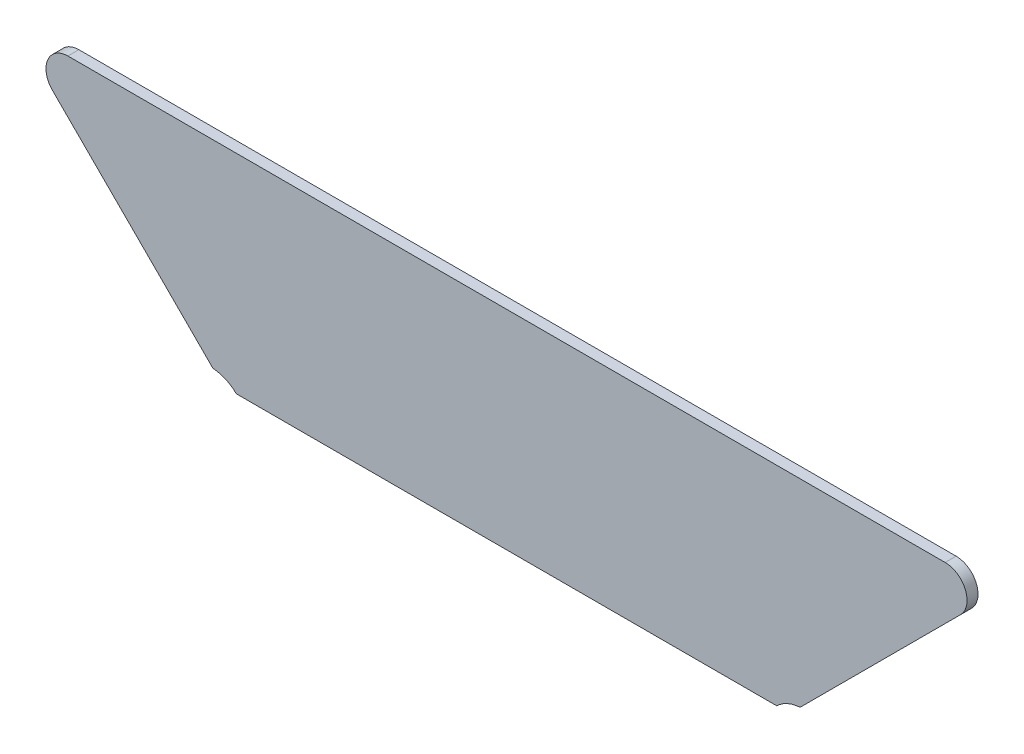
SolidWorks part; units mm, degrees
material "ABS"
ref_plane "Front Plane" through (0, 0, 0) normal (0, 0, 1) x (1, 0, 0)
ref_plane "Top Plane" through (0, 0, 0) normal (0, 1, 0) x (1, 0, 0)
ref_plane "Right Plane" through (0, 0, 0) normal (1, 0, 0) x (0, 0, -1)
sketch "Sketch1" plane through (0, 0, 0) normal (0, 0, 1) x (1, 0, 0)
  line L8 (-10, 99) -> (-90, 99)
  line L9 (-91.4142, 95.5858) -> (-76.7792, 80.9508)
  line L10 (-74.6403, 80) -> (-25.3597, 80)
  line L11 (-23.2208, 80.9508) -> (-8.5858, 95.5858)
  line L12 (-10, 99) -> (-90, 99)
  line L13 (-91.4142, 95.5858) -> (-76.7792, 80.9508)
  line L14 (-74.6403, 80) -> (-25.3597, 80)
  line L15 (-23.2208, 80.9508) -> (-8.5858, 95.5858)
  arc A8 (-90, 99) -> (-91.4142, 95.5858) centre (-90, 97) ccw
  arc A9 (-23.2208, 80.9508) -> (-25.3597, 80) centre (-23, 77.5728) ccw
  arc A10 (-23.2208, 80.9508) -> (-25.3597, 80) centre (-23, 77.5728) ccw
  arc A11 (-8.5858, 95.5858) -> (-10, 99) centre (-10, 97) ccw
  arc A12 (-90, 99) -> (-91.4142, 95.5858) centre (-90, 97) ccw
  arc A15 (-8.5858, 95.5858) -> (-10, 99) centre (-10, 97) ccw
  arc A32 (-74.6403, 80) -> (-76.7792, 80.9508) centre (-77, 77.5728) ccw
  arc A33 (-74.6403, 80) -> (-76.7792, 80.9508) centre (-77, 77.5728) ccw
  dimension "D1" = 0
extrude "Boss-Extrude1" add sketch "Sketch1" along normal blind 1 contours L12 A12 L13 A33 L14 A10 L15 A15
